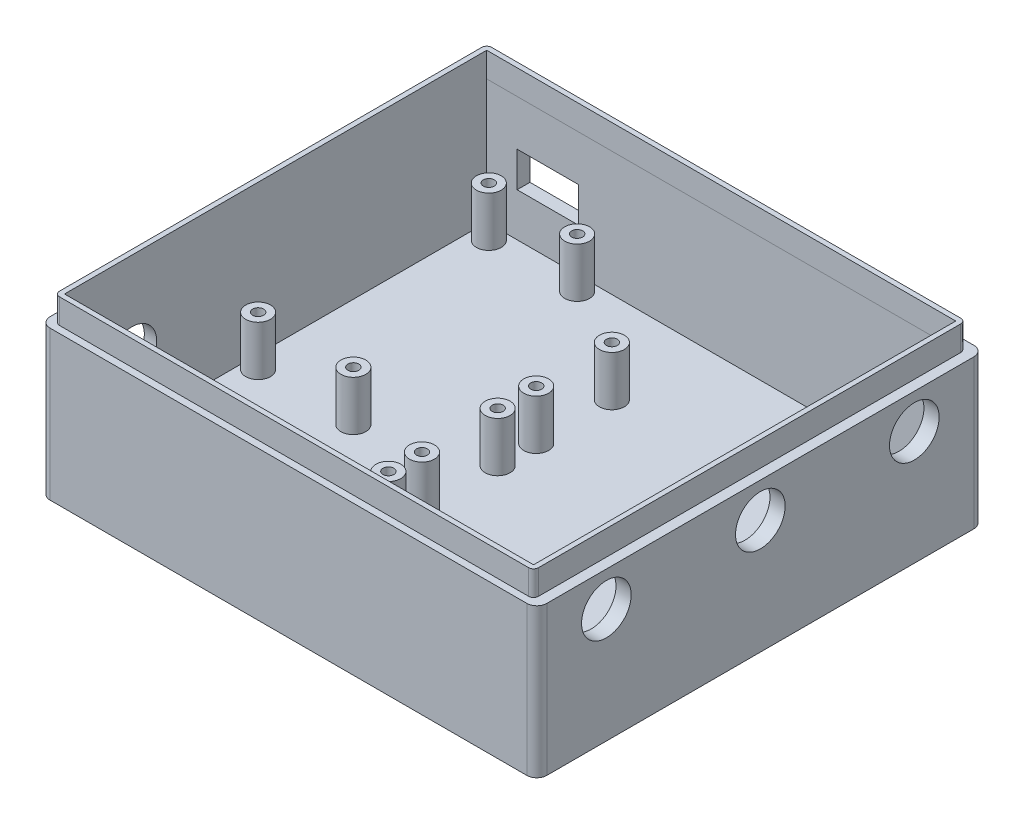
SolidWorks part; units mm, degrees
ref_plane "Front Plane" through (0, 0, 0) normal (0, 0, 1) x (1, 0, 0)
ref_plane "Top Plane" through (0, 0, 0) normal (0, 1, 0) x (1, 0, 0)
ref_plane "Right Plane" through (0, 0, 0) normal (1, 0, 0) x (0, 0, -1)
sketch "Sketch1" plane through (0, 0, 0) normal (0, 1, 0) x (1, 0, 0)
  line L1 (59.9638, -77.9788) -> (-40.0362, -77.9788)
  line L2 (59.9638, -77.9788) -> (59.9638, 12.0212)
  line L3 (59.9638, 12.0212) -> (-40.0362, 12.0212)
  line L4 (-40.0362, -77.9788) -> (-40.0362, 12.0212)
  line L5 (59.9638, -77.9788) -> (-40.0362, 12.0212) construction
  line L6 (59.9638, 12.0212) -> (-40.0362, -77.9788) construction
  point P0 (9.9638, -32.9788)
  dimension "D1" = 90
  dimension "D2" = 100
extrude "Boss-Extrude1" add sketch "Sketch1" along normal blind 30
sketch "Sketch2" plane through (0, 30, 0) normal (0, 1, 0) x (1, 0, 0)
  line L0 (9.9638, 12.0212) -> (9.9638, -77.9788) construction
  line L1 (59.9638, 12.0212) -> (-40.0362, 12.0212) construction
  line L2 (-40.0362, -77.9788) -> (59.9638, -77.9788) construction
sketch "Sketch3" plane through (0, 30, 0) normal (0, 1, 0) x (1, 0, 0)
  line L4 (-37.5362, -75.5662) -> (56.8992, -75.5662)
  line L5 (-37.5362, -75.5662) -> (-37.5362, 9.4338)
  line L6 (-37.5362, 9.4338) -> (56.8992, 9.4338)
  line L7 (56.8992, -75.5662) -> (56.8992, 9.4338)
  line L8 (-37.5362, -75.5662) -> (56.8992, 9.4338) construction
  line L9 (-37.5362, 9.4338) -> (56.8992, -75.5662) construction
  point P6 (9.6815, -33.0662)
extrude "Cut-Extrude1" cut sketch "Sketch3" against normal blind 25
fillet "Fillet2" radius 2 4 edges at (-40.0362, 15, 77.9788) (59.9638, 15, 77.9788) (59.9638, 15, -12.0212) (-40.0362, 15, -12.0212)
sketch "Sketch4" plane through (0, 5, 0) normal (0, 1, 0) x (1, 0, 0)
  line L0 (9.6815, 9.4338) -> (9.6815, -75.5662) construction
  line L1 (56.8992, 9.4338) -> (-37.5362, 9.4338) construction
  line L2 (-37.5362, -75.5662) -> (56.8992, -75.5662) construction
  line L3 (10.6815, -75.5662) -> (10.6815, -33.0662) construction
  line L4 (-29.8762, -28.2799) -> (-20.2862, -28.2799) construction
  line L5 (-13.3962, -5.5025) -> (-12.6962, -51.2573) construction
  line L6 (-9.8962, -5.9025) -> (0, -5.9025) construction
  line L7 (6, -20.9025) -> (6, -36.1425) construction
  line L8 (-18.7862, 9.4338) -> (-18.7862, -75.5662) construction
  circle A0 centre (-15.6962, -39.2573) radius 2.5
  circle A1 centre (-16.3962, 6.4975) radius 2.5
  circle A2 centre (-34.8762, -39.2573) radius 2.4936
  circle A3 centre (-34.1762, 6.4975) radius 2.5
  circle A4 centre (6, -8.9025) radius 2.5
  circle A5 centre (6, -24.1425) radius 2.5
  circle A6 centre (6, -47.1425) radius 2.5
  circle A7 centre (6, -31.9025) radius 2.5
  circle A8 centre (6, -69.1425) radius 2.5
  circle A9 centre (6, -53.9025) radius 2.5
  dimension "D1" = 2
  dimension "D2" = 2
extrude "Boss-Extrude2" add sketch "Sketch4" along normal blind 10
sketch "Sketch5" plane through (0, 15, 0) normal (0, 1, 0) x (1, 0, 0)
  circle A0 centre (-16.3962, 6.4975) radius 1.1
  circle A1 centre (-15.6962, -39.2573) radius 1.1
  circle A2 centre (-34.8762, -39.2573) radius 1.1
  circle A3 centre (-34.1762, 6.4975) radius 1.1
  circle A4 centre (6, -8.9025) radius 1.1
  circle A5 centre (6, -24.1425) radius 1.1
  circle A6 centre (6, -31.9025) radius 1.1
  circle A7 centre (6, -47.1425) radius 1.1
  circle A8 centre (6, -53.9025) radius 1.1
  circle A9 centre (6, -69.1425) radius 1.1
extrude "Cut-Extrude2" cut sketch "Sketch5" against normal blind 5
sketch "Sketch7" plane through (0, 30, 0) normal (0, 1, 0) x (1, 0, 0)
  line L8 (-38.5362, 9.4287) -> (-38.5362, -75.5713)
  line L9 (-37.5362, 10.4287) -> (56.8992, 10.4287)
  line L10 (57.8992, 9.4287) -> (57.8992, -75.5713)
  line L11 (-37.5362, -76.5713) -> (56.8992, -76.5713)
  line L12 (-37.5362, 9.4287) -> (56.8992, 9.4287)
  line L13 (56.8992, 9.4287) -> (56.8992, -75.5713)
  line L14 (56.8992, -75.5713) -> (-37.5362, -75.5713)
  line L15 (-37.5362, -75.5713) -> (-37.5362, 9.4287)
  arc A0 (57.8992, 9.4287) -> (56.8992, 10.4287) centre (56.8992, 9.4287) ccw
  arc A1 (57.8992, -75.5713) -> (56.8992, -76.5713) centre (56.8992, -75.5713) cw
  arc A2 (-37.5362, -76.5713) -> (-38.5362, -75.5713) centre (-37.5362, -75.5713) cw
  arc A3 (-38.5362, 9.4287) -> (-37.5362, 10.4287) centre (-37.5362, 9.4287) cw
  dimension "D2" = 1
extrude "Boss-Extrude3" add sketch "Sketch7" along normal blind 5
sketch "Sketch8" plane through (59.9638, 0, 0) normal (1, 0, 0) x (0, 0, -1)
  line L0 (-75.9788, 36) -> (-75.9788, 21) construction
  line L2 (10.0212, 23) -> (-1.9788, 23) construction
  circle A0 centre (-2094.9788, 15) radius 10
  circle A1 centre (-1.9788, 23) radius 5
  circle A2 centre (-32.9788, 23) radius 5
  circle A3 centre (-63.9788, 23) radius 5
  dimension "D1" = 3
extrude "Cut-Extrude3" cut sketch "Sketch8" against normal up to surface (3.0646 mm away) up to face at (56.8992, 25, 33.0687)
sketch "Sketch9" plane through (-40.0362, 0, 0) normal (-1, 0, 0) x (0, 0, 1)
  line L0 (75.9788, 15) -> (62.0101, 15) construction
  line L1 (75.9788, 0) -> (75.9788, 30) construction
  circle A0 centre (62.0101, 17.5) radius 5
extrude "Cut-Extrude4" cut sketch "Sketch9" against normal up to surface (2.5 mm away) up to face at (-37.5362, 25, 33.0687)
sketch "Sketch10" plane through (0, 0, -12.0212) normal (0, 0, -1) x (-1, 0, 0)
  line L0 (19.0888, 20.8059) -> (31.4166, 20.8059)
  line L1 (19.0888, 20.8059) -> (19.0888, 13.7302)
  line L2 (19.0888, 13.7302) -> (31.4166, 13.7302)
  line L3 (31.4166, 20.8059) -> (31.4166, 13.7302)
extrude "Cut-Extrude5" cut sketch "Sketch10" against normal blind 10
